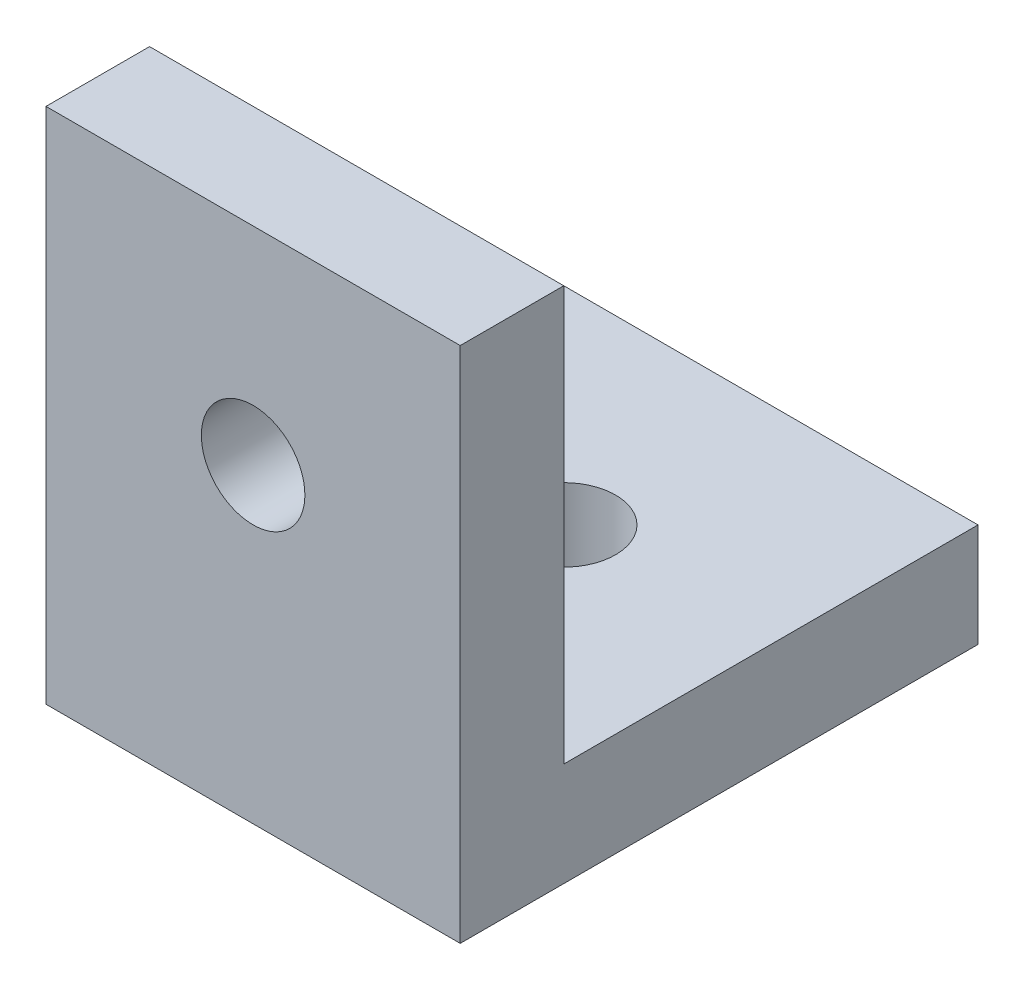
SolidWorks part; units mm, degrees
ref_plane "Front Plane" through (0, 0, 0) normal (0, 0, 1) x (1, 0, 0)
ref_plane "Top Plane" through (0, 0, 0) normal (0, 1, 0) x (1, 0, 0)
ref_plane "Right Plane" through (0, 0, 0) normal (1, 0, 0) x (0, 0, -1)
sketch "Sketch1" plane through (0, 0, 0) normal (1, 0, 0) x (0, 0, -1)
  line L0 (0, 0) -> (0, 25)
  line L1 (0, 25) -> (5, 25)
  line L2 (5, 25) -> (5, 5)
  line L3 (5, 5) -> (25, 5)
  line L4 (25, 5) -> (25, 0)
  line L5 (25, 0) -> (0, 0)
  point P6 (5.1601, 5.6787)
  dimension "D1" = 25
  dimension "D2" = 25
  dimension "D3" = 5
  dimension "D4" = 5
extrude "Boss-Extrude1" add sketch "Sketch1" along normal blind 20
sketch "Sketch2" plane through (0, 5, 0) normal (0, 1, 0) x (1, 0, 0)
  line L0 (10, 25) -> (10, 5) construction
  line L1 (20, 25) -> (0, 25) construction
  line L2 (20, 5) -> (0, 5) construction
  line L3 (0, 15) -> (20, 15) construction
  line L4 (0, 25) -> (0, 5) construction
  line L5 (20, 25) -> (20, 5) construction
  circle A0 centre (10, 15) radius 2.5
  point P14 (0, 0)
  dimension "D1" = 5
extrude "Cut-Extrude1" cut sketch "Sketch2" against normal through all contours A0
sketch "Sketch3" plane through (0, 0, -5) normal (0, 0, -1) x (-1, 0, 0)
  line L0 (-10, 25) -> (-10, 5) construction
  line L1 (-20, 25) -> (0, 25) construction
  line L2 (-20, 5) -> (0, 5) construction
  line L3 (-20, 15) -> (0, 15) construction
  line L4 (-20, 5) -> (-20, 25) construction
  line L5 (0, 5) -> (0, 25) construction
  circle A0 centre (-10, 15) radius 2.5
  point P14 (0, 0)
  dimension "D1" = 5
extrude "Cut-Extrude2" cut sketch "Sketch3" against normal through all
